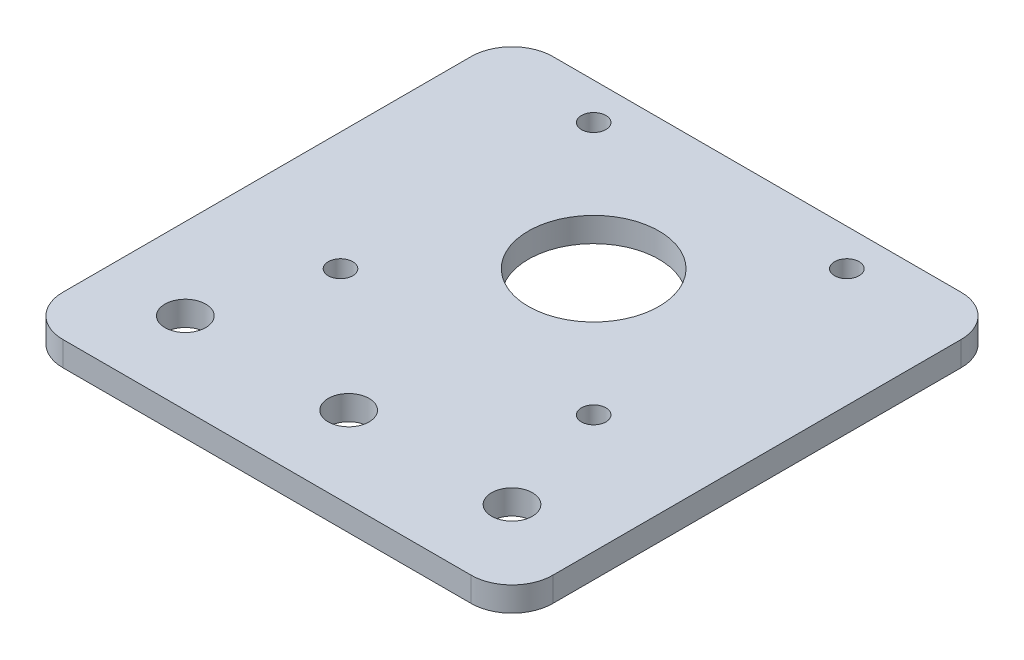
SolidWorks part; units mm, degrees
ref_plane "Front Plane" through (0, 0, 0) normal (0, 0, 1) x (1, 0, 0)
ref_plane "Top Plane" through (0, 0, 0) normal (0, 1, 0) x (1, 0, 0)
ref_plane "Right Plane" through (0, 0, 0) normal (1, 0, 0) x (0, 0, -1)
sketch "Sketch1" plane through (0, 0, 0) normal (0, 1, 0) x (1, 0, 0)
  line L1 (-30, 20) -> (30, 20)
  line L2 (-30, 20) -> (-30, -40)
  line L3 (-30, -40) -> (30, -40)
  line L4 (30, 20) -> (30, -40)
  circle A0 centre (0, 0) radius 8
  dimension "D1" = 16
  dimension "D4" = 20
  dimension "D2" = 60
  dimension "D3" = 60
  dimension "D5" = 30
extrude "Boss-Extrude1" add sketch "Sketch1" along normal blind 3
sketch "Sketch2" plane through (0, 3, 0) normal (0, 1, 0) x (1, 0, 0)
  line L0 (0, 0) -> (39.7425, 0) construction
  line L1 (39.7425, 0) -> (0, 0) construction
  line L2 (0, 0) -> (0, 21.3561) construction
  circle A0 centre (-15.5, 15.5) radius 1.5
  dimension "D1" = 3
  dimension "D2" = 15.5
  dimension "D3" = 15.5
extrude "Cut-Extrude1" cut sketch "Sketch2" against normal through all
pattern_linear "LPattern1" count 2 spacing 31 along (1, 0, 0) count 2 spacing 31 along (0, 0, 1) of "Cut-Extrude1"
sketch "Sketch3" plane through (0, 3, 0) normal (0, 1, 0) x (1, 0, 0)
  line L0 (-30, -40) -> (30, -40) construction
  line L1 (-30, 20) -> (-30, -40) construction
  circle A0 centre (-20, -30) radius 2.5
  dimension "D1" = 5
  dimension "D3" = 10
  dimension "D4" = 10
extrude "Cut-Extrude2" cut sketch "Sketch3" against normal through all
pattern_linear "LPattern2" count 3 spacing 20 along (1, 0, 0) of "Cut-Extrude2"
fillet "Fillet1" radius 5 4 edges at (-30, 1.5, 40) (30, 1.5, -20) (-30, 1.5, -20) (30, 1.5, 40)
